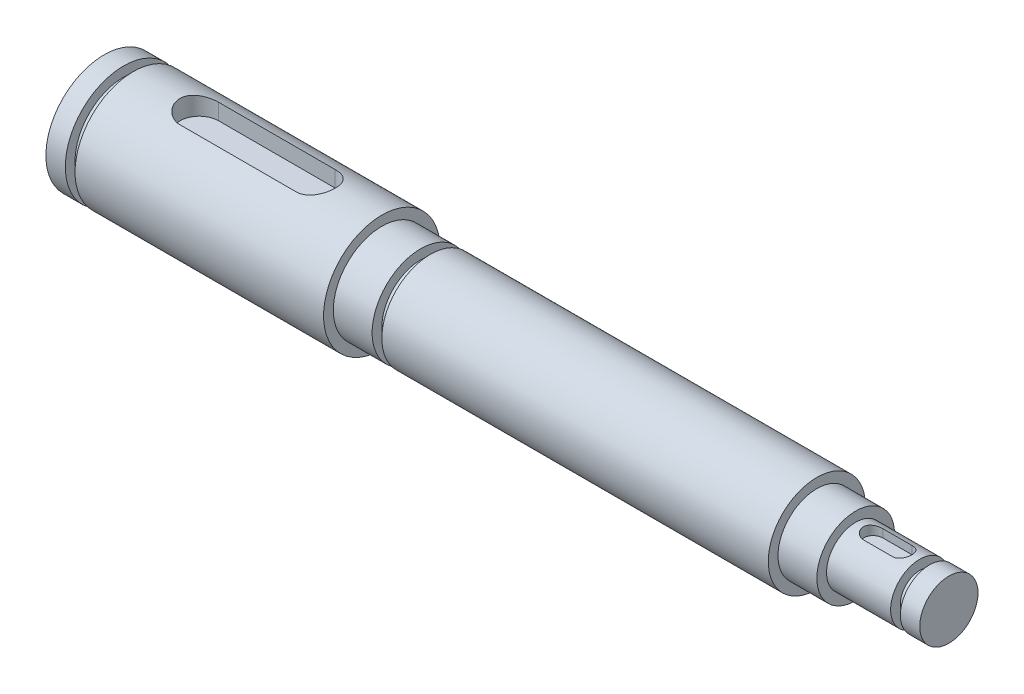
SolidWorks part; units mm, degrees
material "6061 Alloy"
ref_plane "Front Plane" through (0, 0, 0) normal (0, 0, 1) x (1, 0, 0)
ref_plane "Top Plane" through (0, 0, 0) normal (0, 1, 0) x (1, 0, 0)
ref_plane "Right Plane" through (0, 0, 0) normal (1, 0, 0) x (0, 0, -1)
sketch "Sketch2" plane through (0, 0, 0) normal (0, 0, 1) x (1, 0, 0)
  line L0 (0, 0) -> (138.1125, 0)
  line L1 (0, 0) -> (0, 9.525)
  line L2 (0, 9.525) -> (3.175, 9.525)
  line L3 (3.175, 9.525) -> (3.175, 7.9375)
  line L4 (3.175, 7.9375) -> (4.7625, 7.9375)
  line L5 (4.7625, 7.9375) -> (4.7625, 9.525)
  line L6 (4.7625, 9.525) -> (45.4025, 9.525)
  line L7 (45.4025, 9.525) -> (45.4025, 7.9375)
  line L8 (45.4025, 7.9375) -> (51.7525, 7.9375)
  line L9 (116.5225, 7.9375) -> (116.5225, 6.35)
  line L10 (122.8725, 4.7625) -> (133.35, 4.7625)
  line L11 (138.1125, 4.7625) -> (138.1125, 0)
  line L12 (0, 0) -> (-4.1296, 0) construction
  line L13 (51.7525, 7.9375) -> (51.7525, 6.35)
  line L14 (51.7525, 6.35) -> (53.34, 6.35)
  line L15 (53.34, 6.35) -> (53.34, 7.9375)
  line L16 (53.34, 7.9375) -> (116.5225, 7.9375)
  line L17 (133.35, 4.7625) -> (133.35, 3.175)
  line L18 (133.35, 3.175) -> (134.9375, 3.175)
  line L19 (134.9375, 3.175) -> (134.9375, 4.7625)
  line L20 (134.9375, 4.7625) -> (138.1125, 4.7625)
  line L21 (116.5225, 6.35) -> (122.8725, 6.35)
  line L22 (122.8725, 6.35) -> (122.8725, 4.7625)
  point P3 (3.175, 8.7312)
  dimension "D1" = 1.5875
  dimension "D2" = 3.175
  dimension "D3" = 40.64
  dimension "D4" = 71.12
  dimension "D5" = 1.5875
  dimension "D6" = 6.35
  dimension "D7" = 12.7
  dimension "D8" = 19.05
  dimension "D9" = 1.5875
  dimension "D10" = 15.875
  dimension "D11" = 1.5875
  dimension "D12" = 9.525
  dimension "D13" = 1.5875
  dimension "D14" = 1.5875
  dimension "D15" = 3.175
  dimension "D16" = 6.35
revolve "Revolve1" add sketch "Sketch2" angle 360 about L12
ref_plane "Plane1" through (0, 9.525, 0) normal (0, 1, 0) x (1, 0, 0)
sketch "Sketch3" plane through (0, 9.525, 0) normal (0, 1, 0) x (1, 0, 0)
  line L0 (15.5575, 0) -> (34.6075, 0) construction
  line L1 (15.5575, 3.175) -> (34.6075, 3.175)
  line L2 (15.5575, -3.175) -> (34.6075, -3.175)
  line L3 (25.0825, 0) -> (25.0825, 4.3416) construction
  line L4 (45.4025, -9.525) -> (45.4025, 9.525) construction
  line L5 (4.7625, 9.525) -> (4.7625, -9.525) construction
  arc A0 (15.5575, 3.175) -> (15.5575, -3.175) centre (15.5575, 0) ccw
  arc A1 (34.6075, -3.175) -> (34.6075, 3.175) centre (34.6075, 0) ccw
  point P3 (25.0825, 0)
  dimension "D1" = 3.175
  dimension "D2" = 19.05
extrude "Cut-Extrude1" cut sketch "Sketch3" against normal blind 3.175
ref_plane "Plane2" through (0, 4.7625, 0) normal (0, 1, 0) x (1, 0, 0)
sketch "Sketch4" plane through (0, 4.7625, 0) normal (0, 1, 0) x (1, 0, 0)
  line L0 (125.73, 0) -> (130.4925, 0) construction
  line L1 (125.73, 1.5875) -> (130.4925, 1.5875)
  line L2 (125.73, -1.5875) -> (130.4925, -1.5875)
  line L3 (128.1112, 0) -> (128.1112, 1.5875) construction
  line L4 (122.8725, -6.35) -> (122.8725, 6.35) construction
  line L5 (133.35, -3.175) -> (133.35, 3.175) construction
  arc A0 (125.73, 1.5875) -> (125.73, -1.5875) centre (125.73, 0) ccw
  arc A1 (130.4925, -1.5875) -> (130.4925, 1.5875) centre (130.4925, 0) ccw
  point P3 (128.1112, 0)
  dimension "D1" = 3.175
  dimension "D2" = 4.7625
extrude "Cut-Extrude2" cut sketch "Sketch4" against normal blind 1.5875
